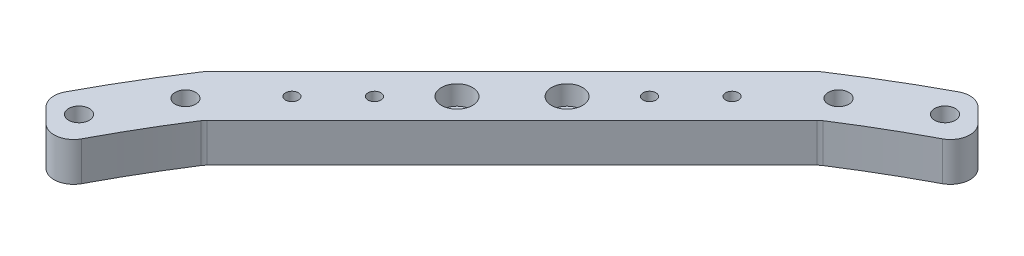
SolidWorks part; units mm, degrees
material "POM 乙缩醛共聚物"
ref_plane "前视基准面" through (0, 0, 0) normal (0, 0, 1) x (1, 0, 0)
ref_plane "上视基准面" through (0, 0, 0) normal (0, 1, 0) x (1, 0, 0)
ref_plane "右视基准面" through (0, 0, 0) normal (1, 0, 0) x (0, 0, -1)
sketch "草图1" plane through (0, 0, 0) normal (0, 1, 0) x (1, 0, 0)
  line L0 (0, 0) -> (275, 0) construction
  line L1 (0, 0) -> (0, 275) construction
  line L2 (0, 0) -> (194.4544, 194.4544) construction
  circle A0 centre (0, 0) radius 255
  circle A1 centre (0, 0) radius 275
  dimension "D1" = 510
  dimension "D2" = 20
  dimension "D3" = 45
extrude "凸台-拉伸1" add sketch "草图1" along normal blind 10
sketch "草图2" plane through (0, 10, 0) normal (0, 1, 0) x (1, 0, 0)
  line L0 (0, 0) -> (275, 0) construction
  line L1 (164.7559, 164.7559) -> (217.7889, 111.7229) construction
  line L2 (164.7559, 164.7559) -> (111.7229, 217.7889) construction
  line L3 (0, 0) -> (164.7559, 164.7559) construction
  line L4 (111.7229, 217.7889) -> (121.6224, 227.6884) construction
  line L5 (217.7889, 111.7229) -> (227.6884, 121.6224) construction
  line L6 (0, 0) -> (240.1716, 111.9938) construction
  line L7 (0, 0) -> (111.9938, 240.1716) construction
  line L8 (0, 0) -> (0, 275) construction
  line L9 (0, 185) -> (30, 185)
  line L10 (-110.5251, 257.2629) -> (-25.4233, 200)
  line L11 (111.9938, 240.1716) -> (30, 185)
  line L12 (0, 200) -> (-25.4233, 200)
  line L13 (240.1716, 111.9938) -> (185, 30)
  line L14 (185, 0) -> (185, 30)
  line L15 (-111.9938, 240.1716) -> (-30, 185)
  line L16 (0, 200) -> (25.4233, 200)
  line L17 (110.5251, 257.2629) -> (25.4233, 200)
  line L18 (257.2629, 110.5251) -> (200, 25.4233)
  line L19 (200, 0) -> (200, 25.4233)
  line L20 (0, 185) -> (-30, 185)
  line L21 (0, 185) -> (-30, 185) construction
  line L22 (0, 200) -> (-30, 200) construction
  line L23 (200, 0) -> (200, -1.5596) construction
  line L24 (185, 0) -> (185, -1.5596) construction
  line L25 (-200, -25.4233) -> (-200, 25.4233)
  line L26 (-257.2629, 110.5251) -> (-200, 25.4233)
  line L27 (-185, -30) -> (-185, 30)
  line L28 (-240.1716, 111.9938) -> (-185, 30)
  line L29 (185, 0) -> (185, -30)
  line L30 (200, 0) -> (200, -25.4233)
  line L31 (257.2629, -110.5251) -> (200, -25.4233)
  line L32 (240.1716, -111.9938) -> (185, -30)
  line L33 (164.7559, -164.7559) -> (111.7229, -217.7889) construction
  line L34 (110.5251, -257.2629) -> (25.4233, -200)
  line L35 (111.9938, -240.1716) -> (30, -185)
  line L36 (0, -185) -> (-30, -185)
  line L37 (0, -200) -> (-25.4233, -200)
  line L38 (0, -200) -> (25.4233, -200)
  line L39 (0, -185) -> (30, -185)
  line L40 (-111.9938, -240.1716) -> (-30, -185)
  line L41 (-110.5251, -257.2629) -> (-25.4233, -200)
  line L42 (-240.1716, -111.9938) -> (-185, -30)
  line L43 (-257.2629, -110.5251) -> (-200, -25.4233)
  circle A0 centre (0, 0) radius 275 construction
  arc A2 (111.9938, 240.1716) -> (240.1716, 111.9938) centre (0, 0) cw
  arc A3 (110.5251, 257.2629) -> (257.2629, 110.5251) centre (0, 0) cw
  arc A4 (-110.5251, 257.2629) -> (-257.2629, 110.5251) centre (0, 0) ccw
  arc A5 (-111.9938, 240.1716) -> (-240.1716, 111.9938) centre (0, 0) ccw
  arc A6 (110.5251, -257.2629) -> (257.2629, -110.5251) centre (0, 0) ccw
  arc A7 (111.9938, -240.1716) -> (240.1716, -111.9938) centre (0, 0) ccw
  arc A8 (-111.9938, -240.1716) -> (-240.1716, -111.9938) centre (0, 0) cw
  arc A9 (-110.5251, -257.2629) -> (-257.2629, -110.5251) centre (0, 0) cw
  point P60 (-185, 0)
  point P61 (-200, 0)
  dimension "D5" = 14
  dimension "D7" = 265
  dimension "D1" = 233
  dimension "D3" = 75
  dimension "D4" = 75
  dimension "D6" = 14
  dimension "D8" = 15
  dimension "D9" = 20
  dimension "D10" = 30
  dimension "D11" = 185
extrude "凸台-拉伸2" add sketch "草图2" along normal blind 10 separate body
sketch "草图8" plane through (0, 20, 0) normal (0, 1, 0) x (1, 0, 0)
  line L0 (0, 0) -> (-187.3833, 187.3833) construction
  line L1 (-243.7881, 137.7221) -> (-232.755, 126.689) construction
  line L2 (-137.7221, 243.7881) -> (-126.689, 232.755) construction
  line L3 (0, 0) -> (0, 200) construction
  line L4 (25.4233, 200) -> (-25.4233, 200) construction
  line L5 (-75, 233.3589) -> (-75, 215.2794) construction
  line L6 (75, 233.3589) -> (75, 215.2794) construction
  line L7 (-30, 185) -> (-111.9938, 240.1716) construction
  line L8 (-25.4233, 200) -> (-110.5251, 257.2629) construction
  line L9 (0, 0) -> (214.4019, 0) construction
  line L10 (200, -25.4233) -> (200, 25.4233) construction
  line L11 (-27.7116, 192.5) -> (-110.5251, 248.2231) construction
  line L12 (-10, 192.5) -> (-27.7116, 192.5) construction
  line L13 (-110.5251, 257.2629) -> (-110.5251, 248.2231) construction
  line L14 (-257.2629, 110.5251) -> (-248.2231, 110.5251) construction
  line L15 (-192.5, 27.7116) -> (-248.2231, 110.5251) construction
  line L16 (-233.3589, 75) -> (-215.2794, 75) construction
  line L17 (233.3589, 75) -> (215.2794, 75) construction
  line L18 (192.5, 27.7116) -> (248.2231, 110.5251) construction
  line L19 (257.2629, 110.5251) -> (248.2231, 110.5251) construction
  line L20 (243.7881, 137.7221) -> (232.755, 126.689) construction
  line L21 (137.7221, 243.7881) -> (126.689, 232.755) construction
  line L22 (0, 0) -> (187.3833, 187.3833) construction
  line L23 (110.5251, 257.2629) -> (110.5251, 248.2231) construction
  line L24 (27.7116, 192.5) -> (110.5251, 248.2231) construction
  line L25 (75, 233.3589) -> (75, 215.2794) construction
  arc A0 (-111.9938, 240.1716) -> (-240.1716, 111.9938) centre (0, 0) ccw construction
  arc A1 (-110.5251, 257.2629) -> (-257.2629, 110.5251) centre (0, 0) ccw construction
  circle A2 centre (-10, 192.5) radius 2.65
  circle A3 centre (10, 192.5) radius 2.65
  circle A4 centre (-10, -192.5) radius 2.65
  circle A5 centre (10, -192.5) radius 2.65
  circle A6 centre (192.5, 10) radius 2.65
  circle A8 centre (192.5, -10) radius 2.65
  circle A9 centre (-192.5, 10) radius 2.65
  circle A10 centre (-192.5, -10) radius 2.65
  circle A11 centre (-110.5251, 248.2231) radius 1.65
  circle A12 centre (-27.7116, 192.5) radius 2.15
  circle A13 centre (-44.3049, 203.6652) radius 2.15
  circle A14 centre (-56.7499, 212.0391) radius 2.15
  circle A15 centre (-69.1949, 220.413) radius 2.15
  circle A16 centre (-81.6399, 228.787) radius 2.15
  arc A17 (-238.2716, 132.2055) -> (-128.8116, 240.1233) centre (0, 0) cw construction
  circle A18 centre (-146.077, 230.0286) radius 2.65
  circle A19 centre (-164.4155, 217.2997) radius 2.65
  circle A20 centre (-183.6389, 201.3166) radius 2.65
  circle A21 centre (-201.3166, 183.6389) radius 2.65
  circle A22 centre (-217.2997, 164.4155) radius 2.65
  circle A23 centre (-230.0286, 146.077) radius 2.65
  circle A24 centre (-128.8116, 240.1233) radius 2.65
  circle A25 centre (-240.1233, 128.8116) radius 2.65
  circle A26 centre (-228.787, 81.6399) radius 2.15
  circle A27 centre (-220.413, 69.1949) radius 2.15
  circle A28 centre (-212.0391, 56.7499) radius 2.15
  circle A29 centre (-203.6652, 44.3049) radius 2.15
  circle A30 centre (-192.5, 27.7116) radius 2.15
  circle A31 centre (-248.2231, 110.5251) radius 1.65
  circle A32 centre (192.5, 27.7116) radius 2.15
  circle A33 centre (248.2231, 110.5251) radius 1.65
  circle A34 centre (203.6652, 44.3049) radius 2.15
  circle A35 centre (212.0391, 56.7499) radius 2.15
  circle A36 centre (220.413, 69.1949) radius 2.15
  circle A37 centre (228.787, 81.6399) radius 2.15
  circle A38 centre (240.1233, 128.8116) radius 2.65
  circle A39 centre (230.0286, 146.077) radius 2.65
  arc A40 (238.2716, 132.2055) -> (128.8116, 240.1233) centre (0, 0) ccw construction
  circle A41 centre (128.8116, 240.1233) radius 2.65
  circle A42 centre (201.3166, 183.6389) radius 2.65
  circle A43 centre (183.6389, 201.3166) radius 2.65
  circle A44 centre (164.4155, 217.2997) radius 2.65
  circle A45 centre (146.077, 230.0286) radius 2.65
  circle A46 centre (81.6399, 228.787) radius 2.15
  circle A47 centre (69.1949, 220.413) radius 2.15
  circle A48 centre (56.7499, 212.0391) radius 2.15
  circle A49 centre (44.3049, 203.6652) radius 2.15
  circle A50 centre (110.5251, 248.2231) radius 1.65
  circle A51 centre (27.7116, 192.5) radius 2.15
  circle A52 centre (217.2997, 164.4155) radius 2.65
  dimension "D1" = 75
  dimension "D3" = 5.3
  dimension "D4" = 20
  dimension "D5" = 7.5
  dimension "D6" = 5.3
  dimension "D7" = 20
  dimension "D8" = 7.5
  dimension "D10" = 3.3
  dimension "D11" = 4.3
  dimension "D12" = 15
  dimension "D13" = 15
  dimension "D14" = 15
  dimension "D15" = 20
  dimension "D16" = 5.3
  dimension "D17" = 20
  dimension "D18" = 25
  dimension "D19" = 20
  dimension "D20" = 25
  dimension "D21" = 25
  dimension "D22" = 5.3
  dimension "D23" = 20
  dimension "D2" = 75
  dimension "D9" = 7.5
extrude "切除-拉伸1" cut sketch "草图8" against normal through all
sketch "草图9" plane through (0, 20, 0) normal (0, 1, 0) x (1, 0, 0)
  line L3 (-128.8133, 248.6104) -> (-117.6534, 237.4504)
  line L4 (0, 0) -> (-187.3833, 187.3833) construction
  line L5 (-248.6104, 128.8133) -> (-237.4504, 117.6534)
  arc A2 (-110.5251, 257.2629) -> (-257.2629, 110.5251) centre (0, 0) ccw construction
  arc A3 (-111.9938, 240.1716) -> (-240.1716, 111.9938) centre (0, 0) ccw construction
  circle A4 centre (-128.8116, 240.1233) radius 2.65 construction
  arc A5 (-128.8133, 248.6104) -> (-248.6104, 128.8133) centre (0, 0) ccw
  arc A6 (-117.6534, 237.4504) -> (-237.4504, 117.6534) centre (0, 0) ccw
  dimension "6" = 6
extrude "切除-拉伸2" cut sketch "草图9" against normal through all flip side to cut
sketch "草图10" plane through (0, 0, 0) normal (0, 0, 1) x (1, 0, 0)
  line L0 (275, 10) -> (-275, 10) construction
  line L1 (388.752, -10) -> (-388.752, -10)
  line L2 (388.752, -10) -> (388.752, 10)
  line L3 (388.752, 10) -> (-388.752, 10)
  line L4 (-388.752, -10) -> (-388.752, 10)
  line L5 (388.752, -10) -> (-388.752, 10) construction
  line L6 (388.752, 10) -> (-388.752, -10) construction
  point P0 (0, 0)
extrude "切除-拉伸3" cut sketch "草图10" against normal through all both and the other way through all
sketch "草图11" plane through (0, 20, 0) normal (0, 1, 0) x (1, 0, 0)
  line L0 (0, 0) -> (-187.3833, 187.3833) construction
  line L2 (-222.7496, 143.5536) -> (-233.5877, 154.3917)
  line L3 (-222.7496, 143.5536) -> (-143.5536, 222.7496)
  line L4 (-154.3917, 233.5877) -> (-233.5877, 154.3917)
  line L7 (-154.3917, 233.5877) -> (-143.5536, 222.7496) construction
  line L8 (-154.3917, 233.5877) -> (-143.5536, 222.7496)
  arc A0 (-117.6534, 237.4504) -> (-237.4504, 117.6534) centre (0, 0) ccw construction
  arc A1 (-128.8133, 248.6104) -> (-248.6104, 128.8133) centre (0, 0) ccw construction
  dimension "D1" = 112
extrude "凸台-拉伸3" add sketch "草图11" against normal up to surface (10 mm away) up to face at (-146.077, 10, -227.3786)
sketch "草图12" plane through (0, 20, 0) normal (0, 1, 0) x (1, 0, 0)
  line L0 (0, 0) -> (-187.3833, 187.3833) construction
  line L1 (-233.5877, 154.3917) -> (-154.3917, 233.5877)
  arc A0 (-128.8133, 248.6104) -> (-248.6104, 128.8133) centre (0, 0) ccw construction
  arc A1 (-154.3917, 233.5877) -> (-233.5877, 154.3917) centre (0, 0) ccw
extrude "切除-拉伸4" cut sketch "草图12" against normal blind 10
sketch "草图13" plane through (0, 20, 0) normal (0, 1, 0) x (1, 0, 0)
  line L0 (-227.3458, 149.564) -> (-149.564, 227.3458) construction
  line L1 (-222.7496, 143.5536) -> (-143.5536, 222.7496) construction
  line L2 (0, 0) -> (-183.1516, 183.1516) construction
  line L3 (-183.1516, 183.1516) -> (-188.4549, 188.4549) construction
  circle A0 centre (-195.5259, 181.3838) radius 1.65
  circle A1 centre (-206.1325, 170.7772) radius 1.65
  circle A2 centre (-216.7391, 160.1706) radius 1.65
  circle A3 centre (-181.3838, 195.5259) radius 1.65
  circle A4 centre (-170.7772, 206.1325) radius 1.65
  circle A5 centre (-160.1706, 216.7391) radius 1.65
  dimension "D3" = 3.3
  dimension "D4" = 20
  dimension "D5" = 15
  dimension "D6" = 15
  dimension "D1" = 7.5
  dimension "D2" = 110
extrude "切除-拉伸5" cut sketch "草图13" against normal up to surface (10 mm away) up to face at (-185.9899, 10, -185.9899)
sketch "草图14" plane through (0, 10, 0) normal (0, -1, 0) x (1, 0, 0)
  circle A0 centre (-181.3838, -195.5259) radius 4
  circle A1 centre (-195.5259, -181.3838) radius 4
  dimension "D1" = 8
extrude "切除-拉伸6" cut sketch "草图14" along normal blind 5 from surface at -10 starting at face at (-160.1706, 20, -218.3891)
fillet "圆角1" radius 5 8 edges at (-143.5536, 15, -222.7496) (-222.7496, 15, -143.5536) (-248.6104, 15, -128.8133) (-237.4504, 15, -117.6534) (-233.5877, 15, -154.3917) (-154.3917, 15, -233.5877) (-128.8133, 15, -248.6104) (-117.6534, 15, -237.4504)
